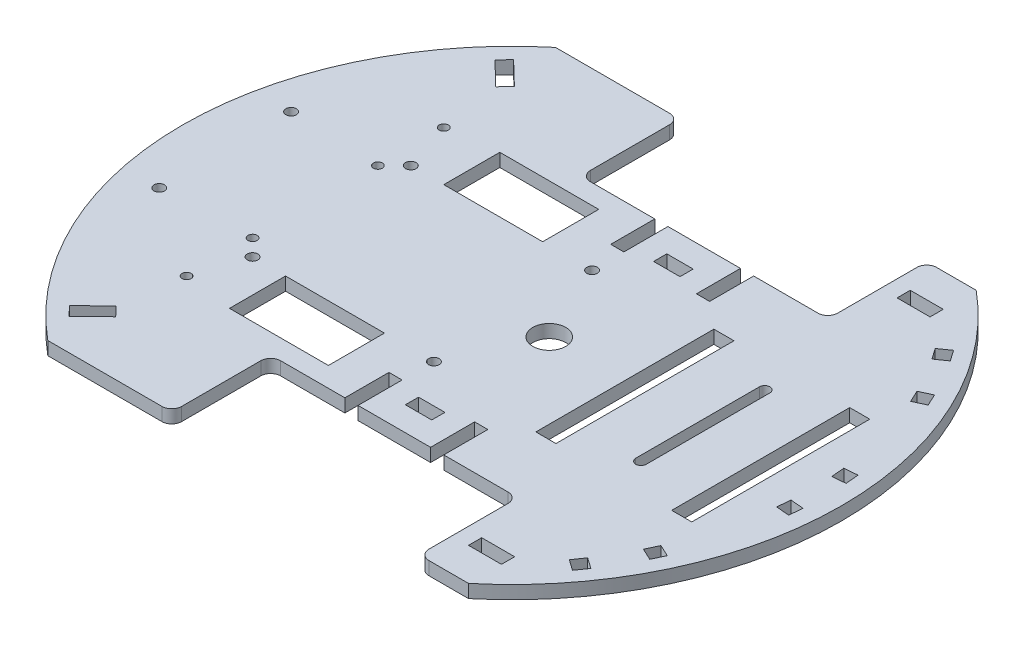
SolidWorks part; units mm, degrees
material "Oak"
ref_plane "Front Plane" through (0, 0, 0) normal (0, 0, 1) x (1, 0, 0)
ref_plane "Top Plane" through (0, 0, 0) normal (0, 1, 0) x (1, 0, 0)
ref_plane "Right Plane" through (0, 0, 0) normal (1, 0, 0) x (0, 0, -1)
sketch "Sketch1" plane through (0, 0, 0) normal (0, 1, 0) x (1, 0, 0)
  line L0 (-63.8044, 77) -> (63.8044, 77)
  line L1 (-63.8044, -77) -> (63.8044, -77)
  circle A0 centre (0, 0) radius 100
  dimension "D1" = 200
  dimension "D2" = 154
extrude "Basis" add sketch "Sketch1" along normal blind 4 contours L1 A0 L0
sketch "Sketch2" plane through (0, 4, 0) normal (0, 1, 0) x (1, 0, 0)
  line L0 (90.817, -6.1912) -> (94.8018, -6.5398)
  line L5 (90.4684, -10.176) -> (90.817, -6.1912)
  line L6 (90.4684, -10.176) -> (94.4532, -10.5246)
  line L7 (94.4532, -10.5246) -> (94.8018, -6.5398)
  line L20 (83.0479, -37.8695) -> (86.6731, -39.56)
  line L21 (81.3574, -41.4948) -> (83.0479, -37.8695)
  line L22 (81.3574, -41.4948) -> (84.9827, -43.1852)
  line L23 (84.9827, -43.1852) -> (86.6731, -39.56)
  line L28 (75.1663, -52.2182) -> (78.4429, -54.5125)
  line L29 (72.872, -55.4948) -> (75.1663, -52.2182)
  line L30 (72.872, -55.4948) -> (76.1486, -57.7891)
  line L31 (76.1486, -57.7891) -> (78.4429, -54.5125)
  line L34 (90.4684, 10.176) -> (94.4532, 10.5246)
  line L35 (90.817, 6.1912) -> (90.4684, 10.176)
  line L36 (90.817, 6.1912) -> (94.8018, 6.5398)
  line L37 (94.8018, 6.5398) -> (94.4532, 10.5246)
  line L50 (81.3574, 41.4948) -> (84.9827, 43.1852)
  line L51 (83.0479, 37.8695) -> (81.3574, 41.4948)
  line L52 (83.0479, 37.8695) -> (86.6731, 39.56)
  line L53 (86.6731, 39.56) -> (84.9827, 43.1852)
  line L58 (72.872, 55.4948) -> (76.1486, 57.7891)
  line L59 (75.1663, 52.2182) -> (72.872, 55.4948)
  line L60 (75.1663, 52.2182) -> (78.4429, 54.5125)
  line L61 (78.4429, 54.5125) -> (76.1486, 57.7891)
  line L64 (-2.896, 0) -> (-129.2077, 0) construction
  arc A3 (60.6142, -73.15) -> (60.6142, 73.15) centre (0, 0) ccw construction
extrude "Modu bracket " cut sketch "Sketch2" against normal up to surface (4 mm away) up to face at (0, 0, 0)
sketch "Sketch3" plane through (0, 4, 0) normal (0, 1, 0) x (1, 0, 0)
  line L0 (-63.8044, -77) -> (63.8044, -77) construction
  line L1 (-26.1956, -77) -> (48.8044, -77)
  line L2 (-26.1956, -77) -> (-26.1956, -47)
  line L3 (-26.1956, -47) -> (48.8044, -47)
  line L4 (48.8044, -77) -> (48.8044, -47)
  line L5 (-63.8044, 77) -> (63.8044, 77) construction
  line L6 (-26.1956, 77) -> (48.8044, 77)
  line L7 (-26.1956, 77) -> (-26.1956, 47)
  line L8 (-26.1956, 47) -> (48.8044, 47)
  line L9 (48.8044, 77) -> (48.8044, 47)
  line L10 (11.3044, -47) -> (11.3044, 47) construction
  line L11 (27.8397, 0) -> (-25.9783, 0) construction
  line L12 (7.8044, -28.15) -> (14.8044, -28.15) construction
  line L13 (7.8044, -28.15) -> (7.8044, -12.65) construction
  line L14 (7.8044, -12.65) -> (14.8044, -12.65) construction
  line L15 (14.8044, -28.15) -> (14.8044, -12.65) construction
  line L16 (7.8044, -28.15) -> (14.8044, -12.65) construction
  line L17 (7.8044, -12.65) -> (14.8044, -28.15) construction
  line L18 (0.8044, -24.15) -> (21.8044, -24.15) construction
  line L19 (0.8044, -24.15) -> (0.8044, -18.65) construction
  line L20 (0.8044, -18.65) -> (21.8044, -18.65) construction
  line L21 (21.8044, -24.15) -> (21.8044, -18.65) construction
  line L22 (0.8044, -24.15) -> (21.8044, -18.65) construction
  line L23 (0.8044, -18.65) -> (21.8044, -24.15) construction
  line L24 (0.8044, 18.65) -> (21.8044, 24.15) construction
  line L25 (0.8044, 24.15) -> (21.8044, 18.65) construction
  line L26 (7.8044, 12.65) -> (14.8044, 28.15) construction
  line L27 (7.8044, 28.15) -> (14.8044, 12.65) construction
  line L28 (21.8044, 24.15) -> (21.8044, 18.65) construction
  line L29 (0.8044, 18.65) -> (21.8044, 18.65) construction
  line L30 (0.8044, 24.15) -> (0.8044, 18.65) construction
  line L31 (0.8044, 24.15) -> (21.8044, 24.15) construction
  line L32 (14.8044, 28.15) -> (14.8044, 12.65) construction
  line L33 (7.8044, 12.65) -> (14.8044, 12.65) construction
  line L34 (7.8044, 28.15) -> (7.8044, 12.65) construction
  line L35 (7.8044, 28.15) -> (14.8044, 28.15) construction
  line L36 (7.3044, 35.65) -> (15.3044, 39.65) construction
  line L37 (7.3044, -39.65) -> (15.3044, -39.65)
  line L38 (7.3044, -39.65) -> (7.3044, -35.65)
  line L39 (7.3044, -35.65) -> (15.3044, -35.65)
  line L40 (15.3044, -39.65) -> (15.3044, -35.65)
  line L41 (7.3044, -39.65) -> (15.3044, -35.65) construction
  line L42 (7.3044, -35.65) -> (15.3044, -39.65) construction
  line L43 (7.3044, 39.65) -> (15.3044, 35.65) construction
  line L44 (15.3044, 39.65) -> (15.3044, 35.65)
  line L45 (7.3044, 35.65) -> (15.3044, 35.65)
  line L46 (7.3044, 39.65) -> (7.3044, 35.65)
  line L47 (7.3044, 39.65) -> (15.3044, 39.65)
  circle A0 centre (11.3044, 0) radius 5
  circle A1 centre (11.3044, -10.15) radius 1.6 construction
  circle A3 centre (11.3044, 10.15) radius 1.6 construction
  point P21 (11.3044, -20.4)
  point P26 (11.3044, -21.4)
  point P42 (11.3044, 21.4)
  point P43 (11.3044, 20.4)
  point P44 (11.3044, -37.65)
  point P53 (11.3044, 37.65)
  point P54 (11.3044, -28.15)
  dimension "D4" = 10
  dimension "D5" = 3.2
  dimension "D1" = 30
  dimension "D2" = 75
  dimension "D3" = 15
  dimension "D6" = 7
  dimension "D7" = 5.5
  dimension "D8" = 4
  dimension "D9" = 21
  dimension "D10" = 6
  dimension "D11" = 2.5
  dimension "D12" = 8
  dimension "D13" = 4
  dimension "D14" = 7.35
  dimension "D15" = 7.5
extrude "Cut-Extrude2" cut sketch "Sketch3" against normal through all contours L1 L4 L3 L2 | L13 L20 L15 L14 | L20 L13 L18 L15 | L20 L19 L18 L13 | L18 L13 L12 L15 | L18 L21 L20 L15 | A0 | A3 | A1 | L29 L34 L33 L32 | L31 L34 L29 L32 | L34 L31 L30 L29 | L35 L34 L31 L32 | L31 L32 L29 L28 | L47 L46 L45 L44 | L9 L6 L7 L8 | L39 L40 L37 L38
sketch "Sketch4" plane through (0, 4, 0) normal (0, 1, 0) x (1, 0, 0)
  line L0 (57.8821, -18.75) -> (57.8821, 18.75) construction
  line L1 (56.2821, -18.75) -> (56.2821, 18.75)
  line L2 (59.4821, -18.75) -> (59.4821, 18.75)
  line L4 (75.4321, -27) -> (81.5321, -27)
  line L5 (75.4321, -27) -> (75.4321, 27)
  line L6 (75.4321, 27) -> (81.5321, 27)
  line L7 (81.5321, -27) -> (81.5321, 27)
  line L8 (57.8821, -38.7193) -> (57.8821, 52.9351) construction
  line L9 (40.3321, 27) -> (34.2321, 27)
  line L10 (34.2321, -27) -> (34.2321, 27)
  line L11 (40.3321, -27) -> (34.2321, -27)
  line L12 (40.3321, -27) -> (40.3321, 27)
  arc A0 (56.2821, -18.75) -> (59.4821, -18.75) centre (57.8821, -18.75) ccw
  arc A1 (59.4821, 18.75) -> (56.2821, 18.75) centre (57.8821, 18.75) ccw
  point P2 (57.8821, 0)
  point P12 (75.4321, 0)
  dimension "D1" = 37.5
  dimension "D2" = 3.2
  dimension "D3" = 54
  dimension "D4" = 15.95
  dimension "D5" = 6.1
extrude "Cut-Extrude3" cut sketch "Sketch4" against normal up to surface (4 mm away) up to face at (11.3044, 0, 37.65)
sketch "Sketch5" plane through (0, 4, 0) normal (0, 1, 0) x (1, 0, 0)
  line L0 (11.3044, -47) -> (11.3044, 47) construction
  line L1 (-3.6956, -47.64) -> (0.3044, -47.64)
  line L2 (-3.6956, -47.64) -> (-3.6956, -33.64)
  line L3 (-3.6956, -33.64) -> (0.3044, -33.64)
  line L4 (0.3044, -47.64) -> (0.3044, -33.64)
  line L5 (-3.6956, 33.64) -> (0.3044, 33.64)
  line L6 (-3.6956, 33.64) -> (-3.6956, 47.64)
  line L7 (-3.6956, 47.64) -> (0.3044, 47.64)
  line L8 (0.3044, 33.64) -> (0.3044, 47.64)
  line L9 (-26.1956, -47) -> (48.8044, -47) construction
  line L10 (-26.1956, 47) -> (48.8044, 47) construction
  line L11 (26.3044, 47.64) -> (22.3044, 47.64)
  line L12 (22.3044, 33.64) -> (22.3044, 47.64)
  line L13 (26.3044, 33.64) -> (22.3044, 33.64)
  line L14 (26.3044, 33.64) -> (26.3044, 47.64)
  line L15 (26.3044, -33.64) -> (22.3044, -33.64)
  line L16 (22.3044, -47.64) -> (22.3044, -33.64)
  line L17 (26.3044, -47.64) -> (22.3044, -47.64)
  line L18 (26.3044, -47.64) -> (26.3044, -33.64)
  dimension "D2" = 14
  dimension "D1" = 4
  dimension "D4" = 22
  dimension "D3" = 13.36
  dimension "D5" = 67.28
extrude "Cut-Extrude4" cut sketch "Sketch5" against normal up to surface (4 mm away) up to face at (37.2821, 0, 0)
sketch "Sketch6" plane through (0, 4, 0) normal (0, 1, 0) x (1, 0, 0)
  line L0 (-95, 0) -> (-54.152, 0) construction
  line L5 (-62.5181, 57.5927) -> (-59.7394, 60.47)
  line L6 (-69.7115, 64.5392) -> (-62.5181, 57.5927)
  line L7 (-66.9328, 67.4166) -> (-69.7115, 64.5392)
  line L8 (-59.7394, 60.47) -> (-66.9328, 67.4166)
  line L9 (-59.7394, -60.47) -> (-62.5181, -57.5927)
  line L10 (53.8044, -67) -> (63.8044, -67)
  line L11 (53.8044, -67) -> (53.8044, -63)
  line L12 (53.8044, -63) -> (63.8044, -63)
  line L13 (63.8044, -67) -> (63.8044, -63)
  line L14 (48.8044, -77) -> (48.8044, -47) construction
  line L15 (48.8044, -77) -> (63.8044, -77) construction
  line L16 (53.8044, 63) -> (63.8044, 63)
  line L17 (63.8044, 67) -> (63.8044, 63)
  line L18 (53.8044, 67) -> (63.8044, 67)
  line L19 (53.8044, 67) -> (53.8044, 63)
  line L20 (-66.9328, -67.4166) -> (-59.7394, -60.47)
  line L21 (-69.7115, -64.5392) -> (-66.9328, -67.4166)
  line L22 (-62.5181, -57.5927) -> (-69.7115, -64.5392)
  circle A0 centre (0, 0) radius 95 construction
  arc A1 (-77.7809, -54.5448) -> (-77.7809, 54.5448) centre (0, 0) cw construction
  arc A2 (-63.8044, 77) -> (-63.8044, -77) centre (0, 0) ccw construction
  dimension "D5" = 5
  dimension "D1" = 10
  dimension "D2" = 4
  dimension "D3" = 5
  dimension "D4" = 10
  dimension "D6" = 44
  dimension "D8" = 10
  dimension "D9" = 4
  dimension "D10" = 44
extrude "Cut-Extrude5" cut sketch "Sketch6" against normal up to surface (4 mm away) up to face at (9.6895, 0, 0)
sketch "Sketch9" plane through (0, 4, 0) normal (0, 1, 0) x (1, 0, 0)
  line L1 (-54.6956, -24) -> (0.3044, -24) construction
  line L2 (-54.6956, -24) -> (-54.6956, 24) construction
  line L3 (-54.6956, 24) -> (0.3044, 24) construction
  line L4 (0.3044, -24) -> (0.3044, 24) construction
  line L5 (-54.6956, -24) -> (0.3044, 24) construction
  line L6 (-54.6956, 24) -> (0.3044, -24) construction
  line L7 (-59.6956, 42.5) -> (-3.6956, 42.5) construction
  line L8 (-59.6956, 42.5) -> (-59.6956, -42.5) construction
  line L9 (-59.6956, -42.5) -> (-3.6956, -42.5) construction
  line L10 (-3.6956, 42.5) -> (-3.6956, -42.5) construction
  line L11 (-59.6956, -19) -> (-3.6956, -19) construction
  line L12 (-59.6956, -19) -> (-59.6956, 39) construction
  line L13 (-59.6956, 39) -> (-3.6956, 39) construction
  line L14 (-3.6956, -19) -> (-3.6956, 39) construction
  line L16 (-3.6956, 47) -> (-3.6956, 33.64) construction
  line L18 (-59.6956, -39) -> (-3.6956, -39) construction
  line L19 (-59.6956, -39) -> (-59.6956, 19) construction
  line L20 (-59.6956, 19) -> (-3.6956, 19) construction
  line L21 (-3.6956, -39) -> (-3.6956, 19) construction
  circle A0 centre (-54.6956, -24) radius 1.6
  circle A1 centre (-54.6956, 24) radius 1.6
  circle A2 centre (0.3044, 24) radius 1.6
  circle A3 centre (0.3044, -24) radius 1.6
  circle A4 centre (-59.6956, 39) radius 1.375
  circle A6 centre (-59.6956, -19) radius 1.375
  circle A7 centre (-59.6956, 19) radius 1.375
  circle A8 centre (-59.6956, -39) radius 1.375
  point P0 (-27.1956, 0)
  point P23 (-3.6956, 0)
  dimension "D1" = 3.2
  dimension "D9" = 2.75
  dimension "D2" = 48
  dimension "D3" = 55
  dimension "D4" = 11
  dimension "D5" = 85
  dimension "D6" = 56
  dimension "D7" = 58
  dimension "D8" = 3.5
  dimension "D10" = 3.5
  dimension "D11" = 58
extrude "Cut-Extrude7" cut sketch "Sketch9" against normal up to surface (4 mm away) up to face at (-64.7254, 0, -62.5046)
sketch "Sketch10" plane through (0, 4, 0) normal (0, 1, 0) x (1, 0, 0)
  line L0 (-100, 0) -> (100, 0) construction
  line L15 (-44.6956, 41) -> (-14.6956, 41)
  line L16 (-44.6956, -24) -> (-14.6956, -24)
  line L17 (-44.6956, -24) -> (-44.6956, -41)
  line L18 (-44.6956, -41) -> (-14.6956, -41)
  line L19 (-14.6956, -24) -> (-14.6956, -41)
  line L20 (-14.6956, 24) -> (-14.6956, 41)
  line L21 (-44.6956, 24) -> (-14.6956, 24)
  line L22 (-44.6956, 24) -> (-44.6956, 41)
  arc A8 (-63.8044, 77) -> (-63.8044, -77) centre (0, 0) ccw construction
  arc A9 (63.8044, -77) -> (63.8044, 77) centre (0, 0) ccw construction
  dimension "D1" = 17
  dimension "D2" = 30
  dimension "D3" = 10
extrude "Cut-Extrude8" cut sketch "Sketch10" against normal up to surface (4 mm away) up to face at (-59.6956, 0, -37.625)
sketch "Sketch11" plane through (0, 4, 0) normal (0, 1, 0) x (1, 0, 0)
  line L0 (-87, -20) -> (-87, 20) construction
  arc A0 (-63.8044, 77) -> (-63.8044, -77) centre (0, 0) ccw construction
  circle A1 centre (-87, -20) radius 1.6
  circle A2 centre (-87, 20) radius 1.6
  point P6 (-87, 0)
  dimension "D2" = 3.2
  dimension "D1" = 40
  dimension "D3" = 87
extrude "Cut-Extrude9" cut sketch "Sketch11" against normal up to surface (4 mm away) up to face at (-29.6956, 0, 32.5)
ref_plane "Plane1" through (0, 16, 0) normal (0, 1, 0) x (1, 0, 0)
fillet "Fillet1" radius 3 8 edges at (48.8044, 2, 77) (48.8044, 2, 47) (-26.1956, 2, 77) (-26.1956, 2, 47) (48.8044, 2, -47) (48.8044, 2, -77) (-26.1956, 2, -77) (-26.1956, 2, -47)
equation "\"WT\"=4"
equation "\"M3_hole\" = 3.2"
equation "\"D5@Sketch3\"=\"M3_hole\""
equation "\"D2@Sketch4\"=\"M3_hole\""
equation "\"D1@Sketch5\"= \"WT\""
equation "\"WIG_OPENING\"=10"
equation "\"D1@Sketch9\"=\"M3_hole\""
equation "\"D2@Sketch11\"=\"M3_hole\""
